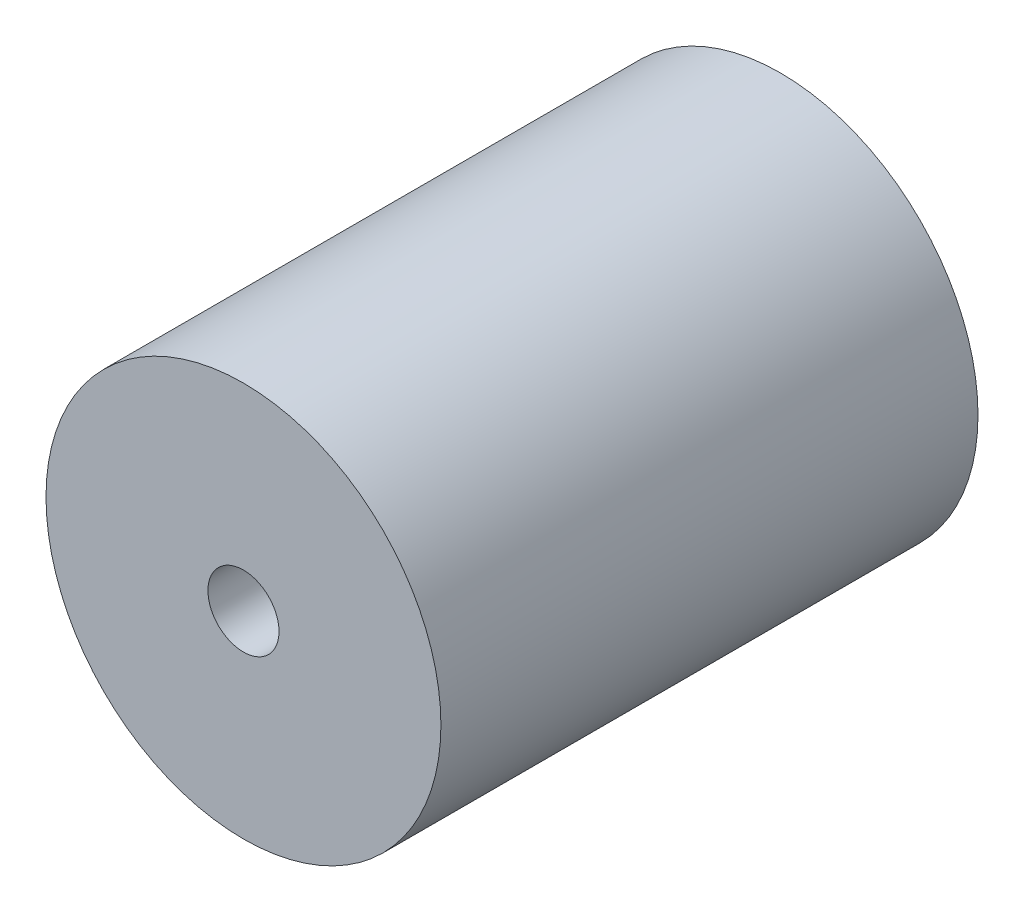
SolidWorks part; units mm, degrees
ref_plane "前视基准面" through (0, 0, 0) normal (0, 0, 1) x (1, 0, 0)
ref_plane "上视基准面" through (0, 0, 0) normal (0, 1, 0) x (1, 0, 0)
ref_plane "右视基准面" through (0, 0, 0) normal (1, 0, 0) x (0, 0, -1)
other "Configuration Table"
sketch "草图1" plane through (0, 0, 0) normal (0, 0, 1) x (1, 0, 0)
  circle A0 centre (0, 0) radius 12.5
  dimension "D1" = 25
extrude "凸台-拉伸1" add sketch "草图1" along normal blind 34
sketch "草图2" plane through (0, 0, 34) normal (0, 0, 1) x (1, 0, 0)
  circle A0 centre (0, 0) radius 2.25
  dimension "D1" = 4.5
extrude "切除-拉伸1" cut sketch "草图2" against normal blind 11
sketch "草图3" plane through (0, 0, 0) normal (0, 0, -1) x (-1, 0, 0)
  circle A0 centre (0, 0) radius 4
  dimension "D1" = 8
extrude "切除-拉伸2" cut sketch "草图3" against normal blind 11
